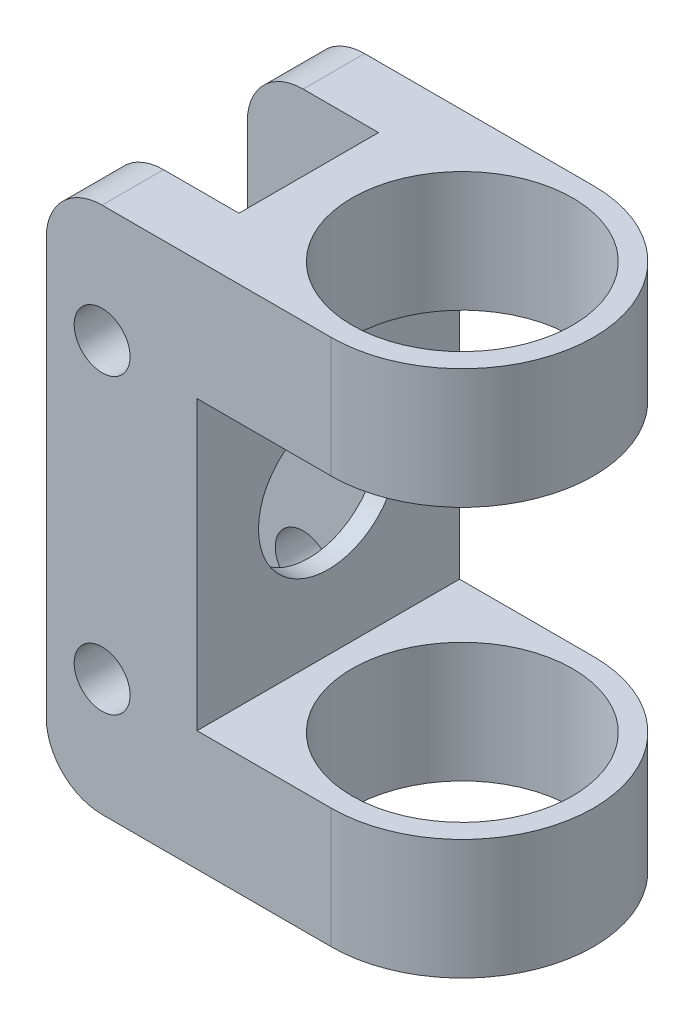
SolidWorks part; units mm, degrees
ref_plane "Front Plane" through (0, 0, 0) normal (0, 0, 1) x (1, 0, 0)
ref_plane "Top Plane" through (0, 0, 0) normal (0, 1, 0) x (1, 0, 0)
ref_plane "Right Plane" through (0, 0, 0) normal (1, 0, 0) x (0, 0, -1)
sketch "Sketch1" plane through (0, 0, 0) normal (0, 1, 0) x (1, 0, 0)
  line L0 (0, 11.938) -> (-25.908, 11.938)
  line L1 (-25.908, 11.938) -> (-25.908, 6.35)
  line L2 (-25.908, 6.35) -> (-13.97, 6.35)
  line L3 (-13.97, 6.35) -> (-13.97, -6.35)
  line L4 (-13.97, -6.35) -> (-25.908, -6.35)
  line L5 (-25.908, -6.35) -> (-25.908, -11.938)
  line L6 (-25.908, -11.938) -> (0, -11.938)
  circle A0 centre (0, 0) radius 10.033
  arc A1 (0, -11.938) -> (0, 11.938) centre (0, 0) ccw
  point P0 (-13.97, 0)
  dimension "D1" = 20.066
  dimension "D3" = 11.938
  dimension "D2" = 5.588
  dimension "D4" = 25.908
  dimension "D5" = 13.97
extrude "Boss-Extrude1" add sketch "Sketch1" along normal mid plane 48.006
sketch "Sketch3" plane through (0, 0, 0) normal (0, 0, 1) x (1, 0, 0)
  line L0 (11.938, -24.003) -> (11.938, 24.003) construction
  line L1 (-12.192, -13.081) -> (11.938, -13.081)
  line L2 (-12.192, -13.081) -> (-12.192, 13.081)
  line L3 (-12.192, 13.081) -> (11.938, 13.081)
  line L4 (11.938, -13.081) -> (11.938, 13.081)
  line L5 (-12.192, -13.081) -> (11.938, 13.081) construction
  line L6 (-12.192, 13.081) -> (11.938, -13.081) construction
  line L8 (-25.908, 24.003) -> (-25.908, -24.003) construction
  circle A0 centre (-20.828, 13.335) radius 2.54
  circle A1 centre (-20.828, -13.335) radius 2.54
  point P0 (-0.127, 0)
  dimension "D3" = 5.08
  dimension "D1" = 26.162
  dimension "D2" = 12.065
  dimension "D4" = 13.335
  dimension "D5" = 13.335
  dimension "D6" = 5.08
extrude "Cut-Extrude1" cut sketch "Sketch3" against normal through all both and the other way through all
sketch "Sketch5" plane through (0, 0, 0) normal (1, 0, 0) x (0, 0, -1)
  circle A0 centre (0, 0) radius 6.35
  dimension "D1" = 12.7
extrude "Cut-Extrude2" cut sketch "Sketch5" against normal through all
fillet "Fillet1" radius 5.08 4 edges at (-25.908, 24.003, -9.144) (-25.908, -24.003, -9.144) (-25.908, -24.003, 9.144) (-25.908, 24.003, 9.144)
equation "\"D5@Sketch3\"=\"D4@Sketch3\""
